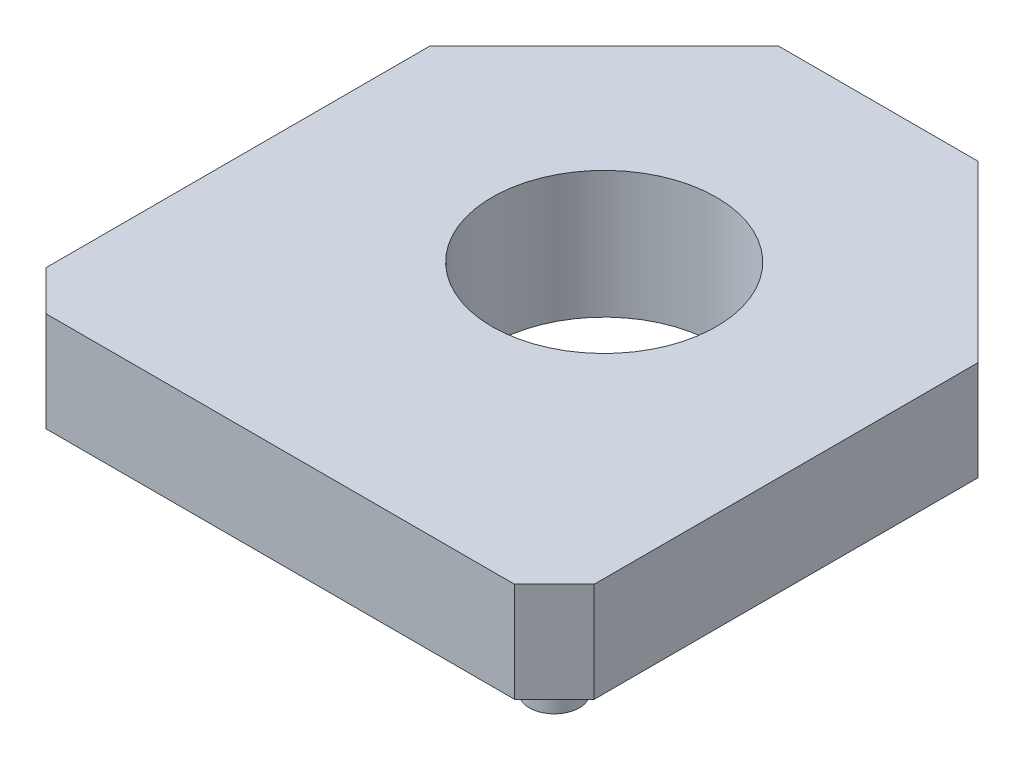
SolidWorks part; units mm, degrees
ref_plane "Front Plane" through (0, 0, 0) normal (0, 0, 1) x (1, 0, 0)
ref_plane "Top Plane" through (0, 0, 0) normal (0, 1, 0) x (1, 0, 0)
ref_plane "Right Plane" through (0, 0, 0) normal (1, 0, 0) x (0, 0, -1)
sketch "Sketch1" plane through (0, 0, 0) normal (0, 1, 0) x (1, 0, 0)
  line L0 (-17.9061, 15.84) -> (-17.9061, 23.54)
  line L1 (-17.9061, 23.54) -> (-14.4061, 27.04)
  line L2 (-14.4061, 27.04) -> (-10.4061, 27.04)
  line L3 (-17.9061, 15.84) -> (-17.1061, 15.04)
  line L4 (-17.1061, 15.04) -> (-7.7061, 15.04)
  line L5 (-12.4061, 15.04) -> (-12.4061, 27.04) construction
  line L6 (-6.9061, 15.84) -> (-7.7061, 15.04)
  line L7 (-6.9061, 15.84) -> (-6.9061, 23.54)
  line L8 (-6.9061, 23.54) -> (-10.4061, 27.04)
  circle A0 centre (-12.4061, 21.54) radius 2.25
  dimension "D8" = 4.5
  dimension "D1" = 12
  dimension "D2" = 45
  dimension "D3" = 45
  dimension "D4" = 5.5
  dimension "D5" = 3.5
  dimension "D6" = 0.8
  dimension "D7" = 5.5
extrude "Boss-Extrude1" add sketch "Sketch1" along normal blind 2
sketch "Sketch2" plane through (0, 0, 0) normal (0, -1, 0) x (1, 0, 0)
  circle A1 centre (-12.4061, -21.54) radius 2.25 construction
  circle A2 centre (-12.4061, -21.54) radius 2.5
  circle A3 centre (-12.4061, -21.54) radius 2.5
  circle A4 centre (-12.4061, -21.54) radius 2.25
  dimension "D1" = 0.25
extrude "Boss-Extrude2" add sketch "Sketch2" along normal blind 0.55
sketch "Sketch3" plane through (0, 0, 0) normal (0, -1, 0) x (1, 0, 0)
  line L0 (-17.9061, -23.54) -> (-17.9061, -15.84) construction
  line L2 (-12.4061, -15.04) -> (-12.4061, -27.04) construction
  line L3 (-17.1061, -15.04) -> (-7.7061, -15.04) construction
  line L4 (-10.4061, -27.04) -> (-14.4061, -27.04) construction
  circle A0 centre (-16.4061, -16.54) radius 0.5
  circle A1 centre (-8.4061, -16.54) radius 0.5
  dimension "D2" = 1
  dimension "D1" = 1.5
  dimension "D3" = 1.5
extrude "Boss-Extrude3" add sketch "Sketch3" along normal blind 1
